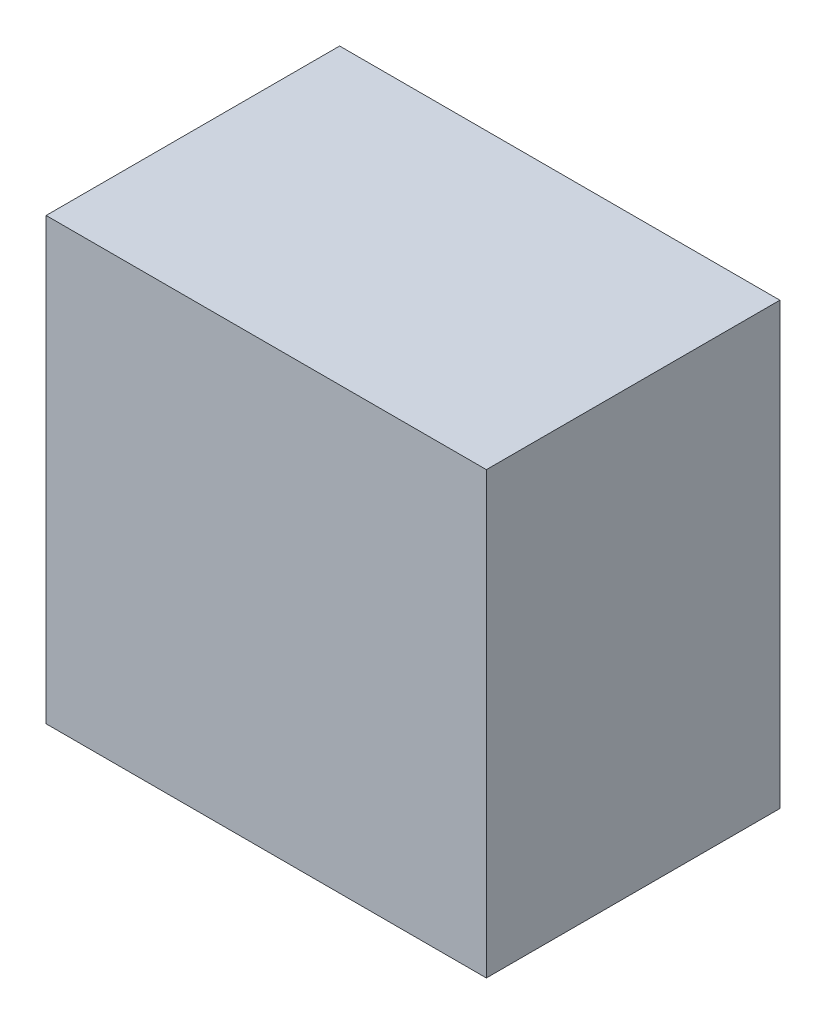
SolidWorks part; units mm, degrees
ref_plane "Front Plane" through (0, 0, 0) normal (0, 0, 1) x (1, 0, 0)
ref_plane "Top Plane" through (0, 0, 0) normal (0, 1, 0) x (1, 0, 0)
ref_plane "Right Plane" through (0, 0, 0) normal (1, 0, 0) x (0, 0, -1)
sketch "Sketch1" plane through (0, 0, 0) normal (0, 0, 1) x (1, 0, 0)
  line L1 (0, 0) -> (30, 0)
  line L2 (0, 0) -> (0, 30)
  line L3 (0, 30) -> (30, 30)
  line L4 (30, 0) -> (30, 30)
extrude "Boss-Extrude1" add sketch "Sketch1" along normal blind 20
